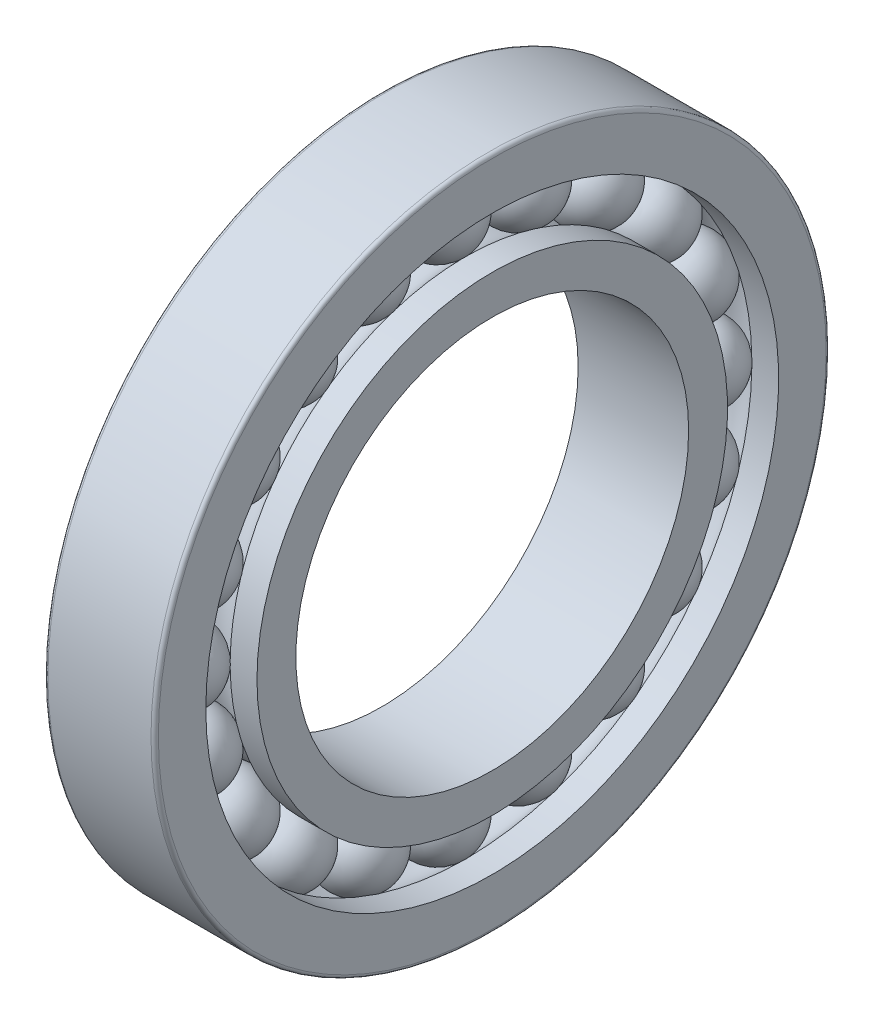
SolidWorks part; units mm, degrees
ref_plane "Front" through (0, 0, 0) normal (0, 0, 1) x (1, 0, 0)
ref_plane "Top" through (0, 0, 0) normal (0, 1, 0) x (1, 0, 0)
ref_plane "Right" through (0, 0, 0) normal (1, 0, 0) x (0, 0, -1)
sketch "Sketch1" plane through (0, 0, 0) normal (0, 0, 1) x (1, 0, 0)
  line L0 (-9.6833, 0) -> (9.8371, 0) construction
  line L1 (-3.125, 21.25) -> (3.125, 21.25)
  line L2 (-4.5966, 21.25) -> (4.6657, 21.25) construction
  arc A0 (3.125, 21.25) -> (-3.125, 21.25) centre (0, 21.25) ccw
  dimension "dia" = 6.25
  dimension "d0" = 42.5
revolve "Revolve1" add sketch "Sketch1" angle 360 about L2
sketch "Sketch2" plane through (0, 0, 0) normal (0, 0, 1) x (1, 0, 0)
  line L0 (-4.5, 19.1667) -> (-4.5, 15)
  line L1 (-4.5, 15) -> (4.5, 15)
  line L2 (4.5, 15) -> (4.5, 19.1667)
  line L3 (4.5, 19.1667) -> (2.3158, 19.1667)
  line L4 (-6.9714, 0) -> (8.1665, 0) construction
  line L5 (-6.7058, 21.25) -> (6.7058, 21.25) construction
  line L6 (-2.3158, 19.1667) -> (-4.5, 19.1667)
  arc A0 (-2.3158, 19.1667) -> (2.3158, 19.1667) centre (0, 21.25) ccw
  dimension "B" = 9
  dimension "B/2" = 4.5
  dimension "D5" = 6.23
  dimension "d" = 30
  dimension "D3" = 21.25
  dimension "D4" = 4.1667
revolve "Revolve2" add sketch "Sketch2" angle 360 about L4
sketch "Sketch3" plane through (0, 0, 0) normal (0, 0, 1) x (1, 0, 0)
  line L0 (-8.7107, 0) -> (9.1288, 0) construction
  line L1 (-4.5, 27.5) -> (4.5, 27.5)
  line L2 (-4.5, 27.5) -> (-4.5, 23.3333)
  line L3 (-4.5, 23.3333) -> (-2.3158, 23.3333)
  line L4 (4.5, 27.5) -> (4.5, 23.3333)
  line L5 (-7.2948, 21.25) -> (7.2948, 21.25) construction
  line L6 (2.3158, 23.3333) -> (4.5, 23.3333)
  arc A0 (2.3158, 23.3333) -> (-2.3158, 23.3333) centre (0, 21.25) ccw
  dimension "D1" = 6.23
  dimension "DD" = 55
  dimension "B" = 9
  dimension "D4" = 21.25
  dimension "D5" = 4.1667
  dimension "B/2" = 4.5
revolve "Revolve3" add sketch "Sketch3" angle 360 about L0
pattern_circular "Circular-Pattern1" count 20 over 360 about axis through (0, 0, 0) along (1, 0, 0) of "Revolve1"
fillet "Fillet1" radius 0.3 4 edges at (-4.5, 0, 15) (-4.5, 0, 27.5) (4.5, 0, 27.5) (4.5, 0, 15)
sketch "Sketch4" plane through (4.5, 0, 0) normal (1, 0, 0) x (0, 0, -1)
  circle A0 centre (0, 0) radius 16
  dimension "D1" = 32
extrude "Cut-Extrude1" cut sketch "Sketch4" against normal up to next
equation "\"d0@Sketch1\" = ( \"DD@Sketch3\" + \"d@Sketch2\" )  / 2"
equation "\"dia@Sketch1\" =  ( \"DD@Sketch3\" - \"d@Sketch2\" )  / 4"
equation "\"D3@Sketch2\" = ( \"DD@Sketch3\" + \"d@Sketch2\" )  / 2 / 2"
equation "\"D4@Sketch2\" = ( \"DD@Sketch3\" - \"d@Sketch2\" )  / 6"
equation "\"D5@Sketch2\" = \"dia@Sketch1\" - 0.02"
equation "\"B/2@Sketch2\" = \"B@Sketch2\" / 2"
equation "\"D4@Sketch3\" = ( \"DD@Sketch3\" + \"d@Sketch2\" )  / 2 / 2"
equation "\"D5@Sketch3\" = ( \"DD@Sketch3\" - \"d@Sketch2\" )  / 6"
equation "\"B@Sketch3\" = \"B@Sketch2\""
equation "\"B/2@Sketch3\" = \"B@Sketch3\" / 2"
equation "\"D1@Sketch3\" = \"dia@Sketch1\" - 0.02"
equation "\"m@Circular-Pattern1\" = int( 3.14159265 / atn(( \"dia@Sketch1\" / 2) / sqr(( \"DD@Sketch3\" + \"d@Sketch2\" )  / 2 * ( \"DD@Sketch3\" + \"d@Sketch2\" )  / 2/4 - ( \"dia@Sketch1\" / 2) *  ( \"dia@Sketch1\" / 2))))-1"
